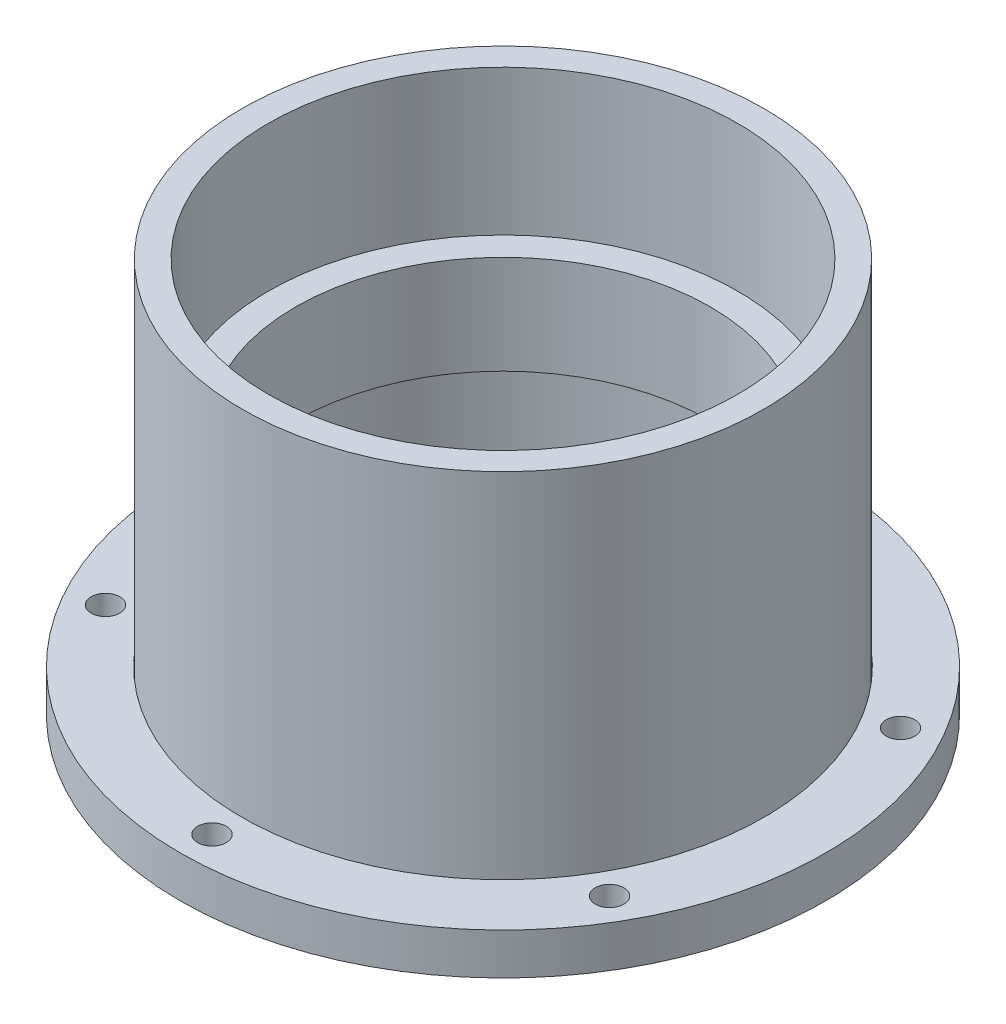
SolidWorks part; units mm, degrees
ref_plane "Front Plane" through (0, 0, 0) normal (0, 0, 1) x (1, 0, 0)
ref_plane "Top Plane" through (0, 0, 0) normal (0, 1, 0) x (1, 0, 0)
ref_plane "Right Plane" through (0, 0, 0) normal (1, 0, 0) x (0, 0, -1)
sketch "Sketch2" plane through (0, 0, 0) normal (0, 1, 0) x (1, 0, 0)
  circle A0 centre (0, 0) radius 45.22
  circle A1 centre (0, 0) radius 50.22
extrude "Boss-Extrude1" add sketch "Sketch2" along normal blind 29
sketch "Sketch3" plane through (0, 29, 0) normal (0, 1, 0) x (1, 0, 0)
  circle A0 centre (0, 0) radius 50.22
  circle A1 centre (0, 0) radius 39.97
  circle A3 centre (0, 0) radius 45.22
  circle M4 centre (0, 0) radius 50.22
  circle M5 centre (0, 0) radius 45.22
extrude "Boss-Extrude2" add sketch "Sketch3" along normal blind 19 contours A1 M5 | M4 M5
sketch "Sketch4" plane through (0, 48, 0) normal (0, 1, 0) x (1, 0, 0)
  circle A0 centre (0, 0) radius 50.22
  circle A1 centre (0, 0) radius 45.22
extrude "Boss-Extrude3" add sketch "Sketch4" along normal blind 28
sketch "Sketch6" plane through (0, 0, 0) normal (0, -1, 0) x (1, 0, 0)
  circle A0 centre (0, 0) radius 62.2
  circle A1 centre (0, 0) radius 50.32
  circle A2 centre (0, 56.06) radius 2.75
  circle A3 centre (0, 0) radius 45.22 construction
  circle A4 centre (-48.5494, 28.03) radius 2.75
  circle A5 centre (-48.5494, -28.03) radius 2.75
  circle A6 centre (48.5494, 28.03) radius 2.75
  circle A7 centre (48.5494, -28.03) radius 2.75
  circle A8 centre (0, -56.06) radius 2.75
  dimension "D1" = 11.88
  dimension "D2" = 56.06
extrude "Boss-Extrude4" add sketch "Sketch6" against normal blind 8
